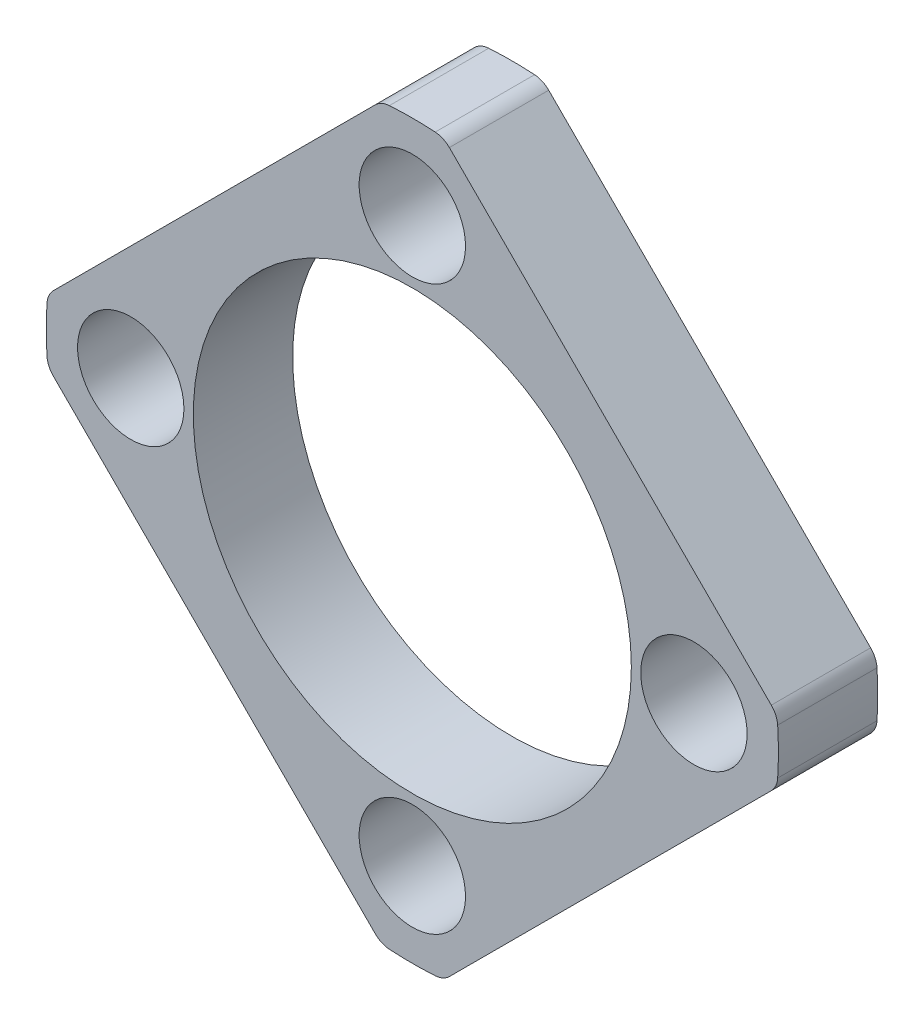
SolidWorks part; units mm, degrees
material "6061-T6 (SS)"
ref_plane "Front Plane" through (0, 0, 0) normal (0, 0, 1) x (1, 0, 0)
ref_plane "Top Plane" through (0, 0, 0) normal (0, 1, 0) x (1, 0, 0)
ref_plane "Right Plane" through (0, 0, 0) normal (1, 0, 0) x (0, 0, -1)
sketch "Sketch1" plane through (0, 0, 0) normal (0, 0, 1) x (1, 0, 0)
  line L0 (-1.1838, 11.4734) -> (-11.4734, 1.1838)
  line L7 (-11.4734, -1.1838) -> (-1.1838, -11.4734)
  line L8 (1.1838, -11.4734) -> (11.4734, -1.1838)
  line L9 (11.4734, 1.1838) -> (1.1838, 11.4734)
  circle A0 centre (0, -9) radius 1.7
  circle A1 centre (-9, 0) radius 1.7
  circle A2 centre (0, 9) radius 1.7
  circle A3 centre (9, 0) radius 1.7
  arc A4 (-11.4734, 1.1838) -> (-11.677, 0.7327) centre (-10.9784, 0.6889) ccw
  arc A5 (-11.677, 0.7327) -> (-11.677, -0.7327) centre (0, 0) ccw
  arc A6 (-11.677, -0.7327) -> (-11.4734, -1.1838) centre (-10.9784, -0.6889) ccw
  arc A7 (-1.1838, -11.4734) -> (-0.7327, -11.677) centre (-0.6889, -10.9784) ccw
  arc A8 (-0.7327, -11.677) -> (0.7327, -11.677) centre (0, 0) ccw
  arc A9 (0.7327, -11.677) -> (1.1838, -11.4734) centre (0.6889, -10.9784) ccw
  arc A10 (11.4734, -1.1838) -> (11.677, -0.7327) centre (10.9784, -0.6889) ccw
  arc A11 (11.677, -0.7327) -> (11.677, 0.7327) centre (0, 0) ccw
  arc A12 (11.677, 0.7327) -> (11.4734, 1.1838) centre (10.9784, 0.6889) ccw
  arc A13 (1.1838, 11.4734) -> (0.7327, 11.677) centre (0.6889, 10.9784) ccw
  arc A14 (0.7327, 11.677) -> (-0.7327, 11.677) centre (0, 0) ccw
  arc A15 (-0.7327, 11.677) -> (-1.1838, 11.4734) centre (-0.6889, 10.9784) ccw
  circle A16 centre (0, 0) radius 7
  point P0 (0, 0)
  dimension "D3" = 3.4
  dimension "D6" = 14
  dimension "D4" = 14.5516
  dimension "D5" = 90
extrude "Boss-Extrude1" add sketch "Sketch1" along normal blind 3.175
